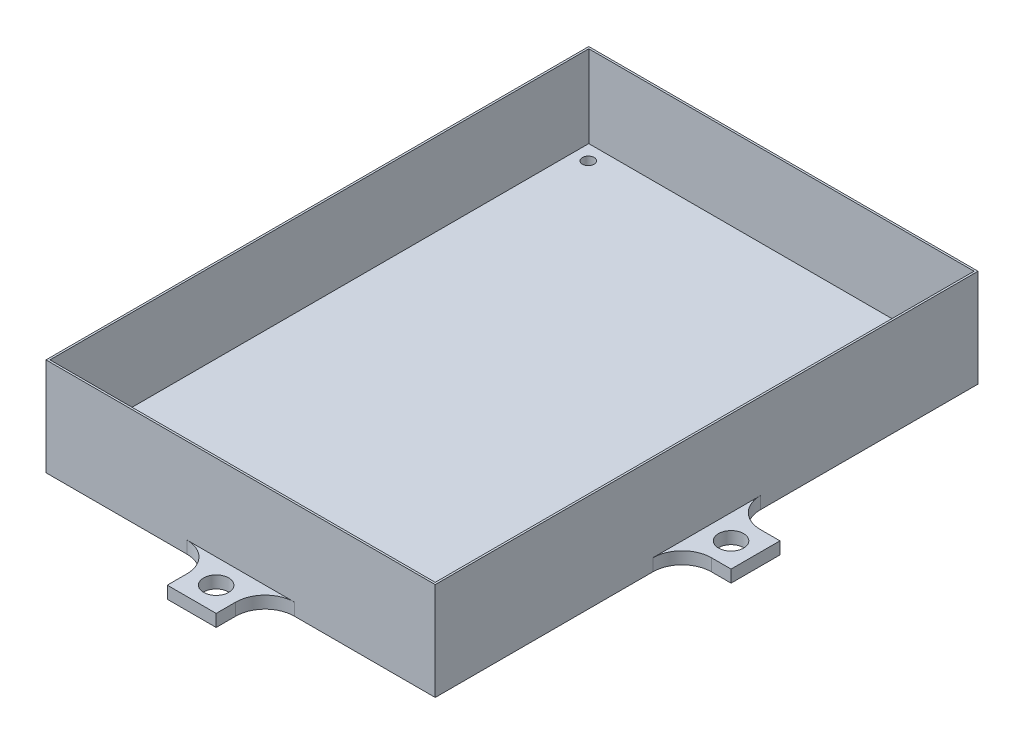
SolidWorks part; units mm, degrees
ref_plane "Front Plane" through (0, 0, 0) normal (0, 0, 1) x (1, 0, 0)
ref_plane "Top Plane" through (0, 0, 0) normal (0, 1, 0) x (1, 0, 0)
ref_plane "Right Plane" through (0, 0, 0) normal (1, 0, 0) x (0, 0, -1)
sketch "Sketch1" plane through (0, 0, 0) normal (0, 1, 0) x (1, 0, 0)
  line L1 (0, 0) -> (101.092, 0)
  line L2 (0, 0) -> (0, 140.97)
  line L3 (0, 140.97) -> (101.092, 140.97)
  line L4 (101.092, 0) -> (101.092, 140.97)
  dimension "D1" = 140.97
  dimension "D2" = 101.092
extrude "Boss-Extrude1" add sketch "Sketch1" along normal blind 25.4
sketch "Sketch2" plane through (0, 25.4, 0) normal (0, 1, 0) x (1, 0, 0)
  line L0 (0, 0) -> (101.092, 0) construction
  line L1 (0.508, 0.508) -> (100.584, 0.508)
  line L2 (0.508, 0.508) -> (0.508, 140.462)
  line L3 (0.508, 140.462) -> (100.584, 140.462)
  line L4 (100.584, 0.508) -> (100.584, 140.462)
  line L5 (0, 140.97) -> (0, 0) construction
  dimension "D1" = 139.954
  dimension "D2" = 100.076
  dimension "D3" = 0.508
  dimension "D4" = 0.508
extrude "Cut-Extrude1" cut sketch "Sketch2" against normal blind 21.336
sketch "Sketch3" plane through (0, 4.064, 0) normal (0, 1, 0) x (1, 0, 0)
  line L0 (0.508, 70.485) -> (100.584, 70.485) construction
  line L1 (0.508, 140.462) -> (0.508, 0.508) construction
  line L2 (100.584, 0.508) -> (100.584, 140.462) construction
  line L3 (50.546, 140.462) -> (50.546, 0) construction
  line L4 (100.584, 140.462) -> (0.508, 140.462) construction
  line L5 (0, 0) -> (101.092, 0) construction
  circle A0 centre (4.318, 136.525) radius 1.524
  circle A1 centre (96.774, 136.525) radius 1.524
  circle A2 centre (96.774, 4.191) radius 1.524
  circle A3 centre (4.318, 4.191) radius 1.524
  point P20 (50.546, 70.231)
  dimension "D1" = 3.048
  dimension "D2" = 66.294
  dimension "D3" = 46.228
  dimension "D4" = 46.228
  dimension "D5" = 66.294
extrude "Cut-Extrude2" cut sketch "Sketch3" against normal blind 21.336
sketch "Sketch4" plane through (0, 0, -140.97) normal (0, 0, -1) x (-1, 0, 0)
  line L1 (-56.896, 0) -> (-44.196, 0)
  line L2 (-56.896, 0) -> (-56.896, 3.175)
  line L3 (-56.896, 3.175) -> (-44.196, 3.175)
  line L4 (-44.196, 0) -> (-44.196, 3.175)
  line L5 (-101.092, 0) -> (0, 0) construction
  line L6 (0, 25.4) -> (0, 0) construction
  dimension "D1" = 3.175
  dimension "D2" = 12.7
  dimension "D3" = 44.196
  dimension "D4" = 0
extrude "Boss-Extrude2" add sketch "Sketch4" along normal blind 12.7
sketch "Sketch10" plane through (0, 3.175, 0) normal (0, 1, 0) x (1, 0, 0)
  line L0 (44.196, 153.67) -> (44.196, 140.97) construction
  line L1 (44.196, 153.67) -> (56.896, 153.67) construction
  point P0 (50.546, 147.32)
  dimension "D1" = 6.35
  dimension "D2" = 6.35
hole_wizard "5/16-18 Tapped Hole1" positions "Sketch10" profile "Sketch9" tap size "5/16-18" standard "ANSI Inch" end condition through all
sketch "Sketch9" plane through (50.546, 3.175, -147.32) normal (1, 0, 0) x (0, 0, 1)
  line L0 (0, 0) -> (0, 3.175)
  line L1 (0, 3.175) -> (3.2639, 3.175)
  line L2 (3.2639, 3.175) -> (3.2639, 0)
  line L5 (3.2639, 0) -> (0, 0)
  line L11 (0, -6.35) -> (0, 107.95) construction
  dimension "Thru Tap Drill Dia." = 6.5278
  dimension "Thru Tap Drill Depth" = 3.175
cosmetic thread "Hole Thread1" parameters "D2"=7.9375
sketch "Sketch5" plane through (0, 3.175, 0) normal (0, 1, 0) x (1, 0, 0)
  line L0 (44.196, 153.67) -> (56.896, 153.67) construction
  line L1 (44.196, 153.67) -> (44.196, 140.97) construction
  circle A0 centre (50.546, 147.32) radius 3.9687
  point P4 (0, 0)
  dimension "D1" = 7.9375
  dimension "D2" = 6.35
  dimension "D3" = 6.35
sketch "Sketch11" plane through (0, 4.064, 0) normal (0, 1, 0) x (1, 0, 0)
  line L0 (0.508, 70.485) -> (101.092, 70.485) construction
  line L1 (0.508, 140.462) -> (0.508, 0.508) construction
  line L2 (101.092, 0) -> (101.092, 140.97) construction
ref_plane "Plane3" through (0, 0, -70.485) normal (0, 0, 1) x (1, 0, 0)
mirror "Mirror1" about plane through (0, 0, -70.485) normal (0, 0, 1) of "5/16-18 Tapped Hole1", "Boss-Extrude2"
cosmetic thread "Hole Thread2" parameters "D2"=7.9375
sketch "Sketch13" plane through (0, 0, 0) normal (-1, 0, 0) x (0, 0, 1)
  line L0 (55.6006, 0) -> (-55.6006, 0) construction
  line L1 (-64.135, 0) -> (-76.835, 0)
  line L2 (-64.135, 0) -> (-64.135, 3.175)
  line L3 (-64.135, 3.175) -> (-76.835, 3.175)
  line L4 (-76.835, 0) -> (-76.835, 3.175)
  line L6 (-140.97, 25.4) -> (-140.97, 0) construction
  point P6 (-70.485, 0)
  dimension "D1" = 3.175
  dimension "D2" = 12.7
  dimension "D3" = 70.485
extrude "Boss-Extrude3" add sketch "Sketch13" along normal blind 12.7
sketch "Sketch16" plane through (0, 3.175, 0) normal (0, 1, 0) x (1, 0, 0)
  line L0 (-12.7, 64.135) -> (-12.7, 76.835) construction
  line L1 (-12.7, 76.835) -> (0, 76.835) construction
  point P0 (-6.35, 70.485)
  dimension "D1" = 6.35
  dimension "D2" = 6.35
hole_wizard "5/16-18 Tapped Hole2" positions "Sketch16" profile "Sketch15" tap size "5/16-18" standard "ANSI Inch" end condition through all
sketch "Sketch15" plane through (-6.35, 3.175, -70.485) normal (1, 0, 0) x (0, 0, 1)
  line L0 (0, 0) -> (0, 3.175)
  line L1 (0, 3.175) -> (3.2639, 3.175)
  line L2 (3.2639, 3.175) -> (3.2639, 0)
  line L5 (3.2639, 0) -> (0, 0)
  line L11 (0, -6.35) -> (0, 107.95) construction
  dimension "Thru Tap Drill Dia." = 6.5278
  dimension "Thru Tap Drill Depth" = 3.175
cosmetic thread "Hole Thread3" parameters "D2"=7.9375
ref_plane "Plane4" through (50.546, 0, 0) normal (-1, 0, 0) x (0, 0, 1)
mirror "Mirror2" about plane through (50.546, 0, 0) normal (-1, 0, 0) of "Boss-Extrude3", "5/16-18 Tapped Hole2"
cosmetic thread "Hole Thread4" parameters "D2"=7.9375
fillet "Fillet1" radius 7.62 8 edges at (44.196, 1.5875, -140.97) (56.896, 1.5875, -140.97) (101.092, 1.5875, -76.835) (101.092, 1.5875, -64.135) (56.896, 1.5875, 0) (44.196, 1.5875, 0) (0, 1.5875, -64.135) (0, 1.5875, -76.835)
